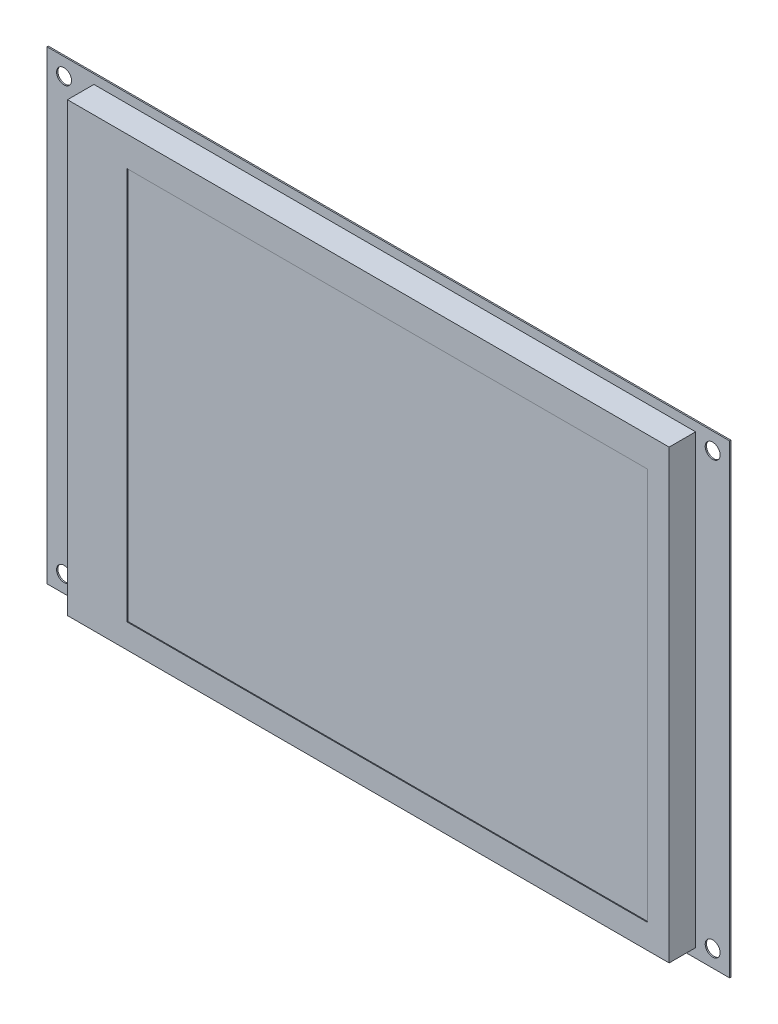
SolidWorks part; units mm, degrees
ref_plane "Front" through (0, 0, 0) normal (0, 0, 1) x (1, 0, 0)
ref_plane "Top" through (0, 0, 0) normal (0, 1, 0) x (1, 0, 0)
ref_plane "Right" through (0, 0, 0) normal (1, 0, 0) x (0, 0, -1)
sketch "Sketch1" plane through (0, 0, 0) normal (0, 0, 1) x (1, 0, 0)
  line L1 (0, 0) -> (141, 0)
  line L2 (0, 0) -> (0, -104.7)
  line L3 (0, -104.7) -> (141, -104.7)
  line L4 (141, 0) -> (141, -104.7)
  dimension "D1" = 141
  dimension "D2" = 104.7
extrude "Extrude1" add sketch "Sketch1" along normal blind 6.2
sketch "Sketch4" plane through (0, 0, 0) normal (0, 0, -1) x (-1, 0, 0)
  line L0 (0, 0) -> (0, -104.7) construction
  line L1 (-149, 2.15) -> (11, 2.15)
  line L2 (-149, 2.15) -> (-149, -106.85)
  line L3 (-149, -106.85) -> (11, -106.85)
  line L4 (11, 2.15) -> (11, -106.85)
  line L5 (0, -104.7) -> (-141, -104.7) construction
  dimension "D1" = 160
  dimension "D2" = 11
  dimension "D3" = 109
  dimension "D4" = 2.15
extrude "Extrude2" add sketch "Sketch4" along normal blind 0.3
sketch "Sketch5" plane through (0, 0, 0) normal (0, 0, 1) x (1, 0, 0)
  line L0 (149, -106.85) -> (-11, -106.85) construction
  line L1 (-11, -106.85) -> (-11, 2.15) construction
  circle A0 centre (145, -1.85) radius 1.75
  circle A1 centre (145, -102.85) radius 1.75
  circle A2 centre (-7, -1.85) radius 1.75
  circle A3 centre (-7, -102.85) radius 1.75
  dimension "D2" = 3.5
  dimension "D3" = 3.5
  dimension "D4" = 3.5
  dimension "D5" = 3.5
  dimension "D1" = 101
  dimension "D6" = 4
  dimension "D7" = 4
  dimension "D8" = 152
extrude "Cut-Extrude1" cut sketch "Sketch5" against normal blind 0.3
sketch "Sketch3" plane through (0, 0, 6.2) normal (0, 0, 1) x (1, 0, 0)
  line L1 (13.9858, -6.9985) -> (135.9858, -6.9985)
  line L2 (13.9858, -6.9985) -> (13.9858, -98.9985)
  line L3 (13.9858, -98.9985) -> (135.9858, -98.9985)
  line L4 (135.9858, -6.9985) -> (135.9858, -98.9985)
  dimension "D1" = 122
  dimension "D2" = 92
extrude "Cut-Extrude4" cut sketch "Sketch3" against normal blind 0.2
